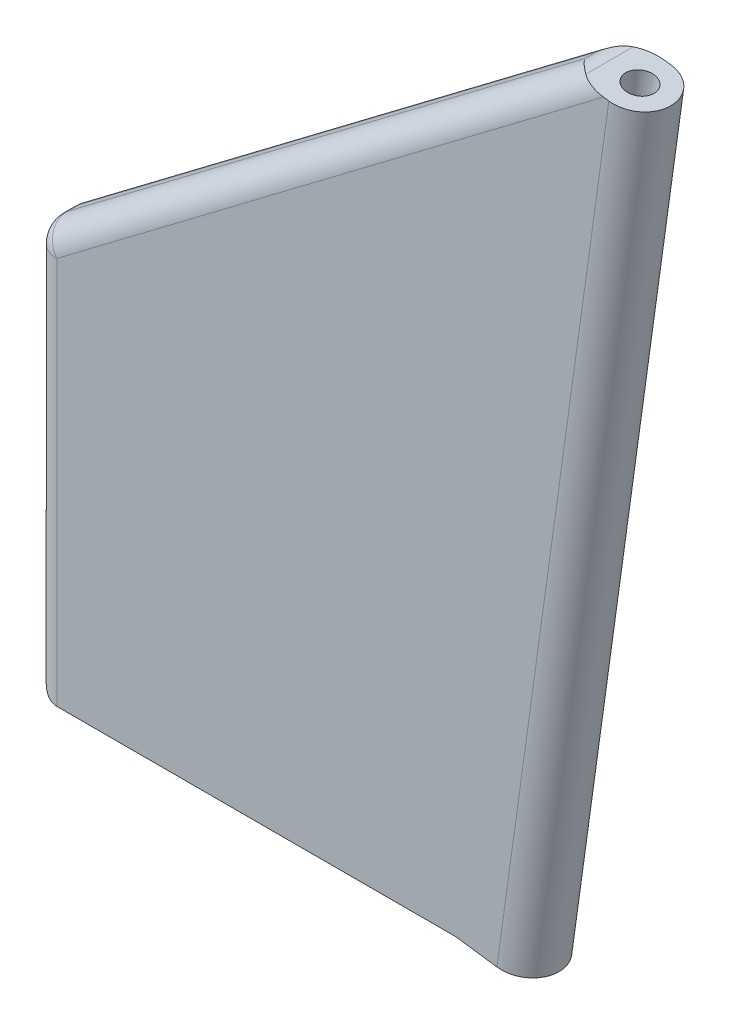
SolidWorks part; units mm, degrees
ref_plane "Front Plane" through (0, 0, 0) normal (0, 0, 1) x (1, 0, 0)
ref_plane "Top Plane" through (0, 0, 0) normal (0, 1, 0) x (1, 0, 0)
ref_plane "Right Plane" through (0, 0, 0) normal (1, 0, 0) x (0, 0, -1)
sketch "Sketch2" plane through (0, 0, 0) normal (0, 0, 1) x (1, 0, 0)
  line L0 (13.439, 209.3871) -> (9.0366, 177.6913)
  line L1 (11.967, 210.6011) -> (14.1601, 210.2965) construction
  line L6 (11.8294, 209.6106) -> (15.0485, 209.1635)
  line L8 (7.4271, 177.9149) -> (10.6462, 177.4678)
  line L9 (7.4271, 177.9149) -> (10.6462, 177.4678)
  line L12 (15.0485, 209.1635) -> (10.6462, 177.4678)
  line L13 (11.8294, 209.6106) -> (7.4271, 177.9149)
  line L14 (7.4271, 177.9149) -> (-9.2729, 177.9149)
  line L16 (-9.2729, 177.9149) -> (-9.2729, 193.6649)
  line L17 (-9.2729, 193.6649) -> (11.8294, 209.6106)
  point P3 (13.198, 207.6526)
  dimension "D4" = 16.7
  dimension "D5" = 15.75
  dimension "D1" = 1
  dimension "D2" = 0
ref_plane "Plane4" through (24.3842, 175.5596, 0) normal (-0.1376, -0.9905, 0) x (-0.9905, 0.1376, 0)
sketch "Sketch4" plane through (24.3842, 175.5596, 0) normal (-0.1376, -0.9905, 0) x (-0.9905, 0.1376, 0)
  line L0 (17.1199, 0) -> (13.8699, 0) construction
  circle A0 centre (15.4949, 0) radius 0.425 construction
  circle A1 centre (15.4949, 0) radius 1.225
  circle A2 centre (15.4949, 0) radius 0.56
  dimension "D1" = 0.85
  dimension "D2" = 0.8
  dimension "D3" = 0.135
extrude "Boss-Extrude1" add sketch "Sketch4" against normal offset from surface (32 mm away) 1
extrude "Boss-Extrude2" add sketch "Sketch2" along normal mid plane 2.45 contours L17 L16 L14 L13 | L6 L13 L9 L0
sketch "Sketch5" plane through (24.3842, 175.5596, 0) normal (-0.1376, -0.9905, 0) x (0.9905, -0.1376, 0)
  circle A2 centre (-15.4949, 0) radius 0.56 construction
  circle A3 centre (-15.4949, 0) radius 0.56
extrude "Cut-Extrude1" cut sketch "Sketch5" against normal up to surface (32 mm away) up to face at (13.7163, 209.3485, 0)
fillet "Fillet1" radius 1 7 edges at (-9.2729, 185.7899, 1.225) (-9.2729, 177.9149, 0) (-9.2729, 185.7899, -1.225) (11.8294, 209.6106, 0) (1.2782, 201.6378, 1.225) (-9.2729, 193.6649, 0) (1.2782, 201.6378, -1.225)
equation "\"D4@Sketch2\"=3.34m /200"
equation "\"D5@Sketch2\"=3.15m /200"
